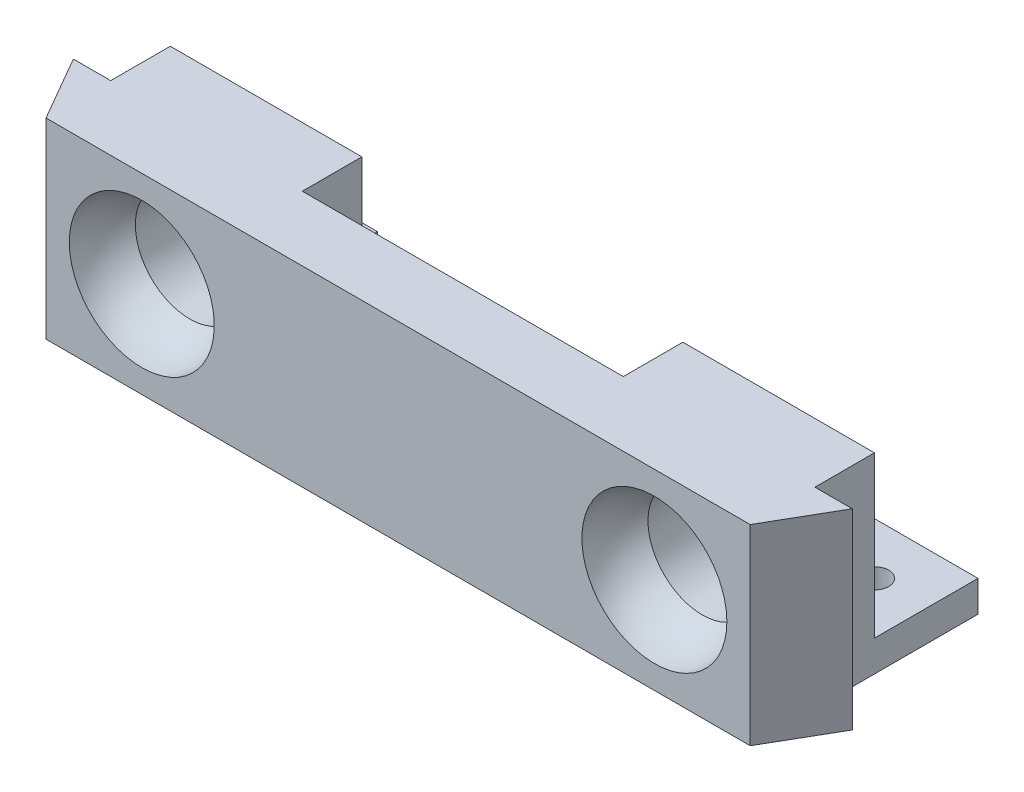
SolidWorks part; units mm, degrees
ref_plane "Front Plane" through (0, 0, 0) normal (0, 0, 1) x (1, 0, 0)
ref_plane "Top Plane" through (0, 0, 0) normal (0, 1, 0) x (1, 0, 0)
ref_plane "Right Plane" through (0, 0, 0) normal (1, 0, 0) x (0, 0, -1)
sketch "Sketch1" plane through (0, 0, 0) normal (0, 1, 0) x (1, 0, 0)
  line L0 (-34, 0) -> (-37.6084, 6.25)
  line L1 (-37.6084, 6.25) -> (-34, 6.25)
  line L2 (37.6084, 6.25) -> (34, 0)
  line L3 (34, 0) -> (-34, 0)
  line L4 (-34, 6.25) -> (-34, 12)
  line L5 (-34, 12) -> (-15.5, 12)
  line L6 (-15.5, 12) -> (-15.5, 6.25)
  line L7 (34, 6.25) -> (34, 12)
  line L8 (34, 12) -> (15.5, 12)
  line L9 (15.5, 12) -> (15.5, 6.25)
  line L11 (34, 6.25) -> (37.6084, 6.25)
  line L12 (-15.5, 6.25) -> (15.5, 6.25)
  dimension "D1" = 6.25
  dimension "D2" = 68
  dimension "D3" = 60
  dimension "D4" = 18.5
  dimension "D5" = 18.5
  dimension "D6" = 5.75
  dimension "D7" = 5.75
extrude "Boss-Extrude1" add sketch "Sketch1" along normal blind 18.5
ref_plane "Plane1" through (0, 9.25, 0) normal (0, 1, 0) x (1, 0, 0)
sketch "Sketch2" plane through (0, 9.25, 0) normal (0, 1, 0) x (1, 0, 0)
  line L0 (-24.75, 35.7158) -> (-24.75, -11.7158) construction
  line L1 (-24.75, 12) -> (-24.75, 0)
  line L2 (-15.5, 12) -> (-34, 12) construction
  line L3 (-24.75, 12) -> (-30, 12)
  line L4 (-30, 12) -> (-30, 4.6301)
  line L5 (-24.75, 0) -> (-31.75, 0)
  line L6 (-34, 0) -> (34, 0) construction
  arc A0 (-31.75, 0) -> (-30, 4.6301) centre (-24.75, 0) cw
  point P4 (-24.75, 12)
  dimension "D3" = 7
  dimension "D1" = 10.5
  dimension "D2" = 14
revolve "Cut-Revolve1" cut sketch "Sketch2" angle 360 about L0
mirror "Mirror1" about plane through (0, 0, 0) normal (1, 0, 0) of "Cut-Revolve1"
sketch "Sketch3" plane through (0, 0, 0) normal (0, 1, 0) x (1, 0, 0)
  line L0 (-34, 12) -> (-34, 22)
  line L1 (-34, 22) -> (-24, 22)
  line L2 (-24, 22) -> (-24, 12)
  line L3 (-15.5, 12) -> (-34, 12) construction
  line L4 (-24, 12) -> (-34, 12)
  line L5 (24, 12) -> (24, 22)
  line L6 (34, 12) -> (15.5, 12) construction
  line L7 (24, 22) -> (34, 22)
  line L8 (34, 22) -> (34, 12)
  line L9 (34, 12) -> (24, 12)
  dimension "D1" = 10
  dimension "D2" = 10
  dimension "D3" = 10
  dimension "D4" = 10
extrude "Boss-Extrude2" add sketch "Sketch3" along normal blind 3
sketch "Sketch5" plane through (0, 3, 0) normal (0, 1, 0) x (1, 0, 0)
  line L0 (-34, 22) -> (-34, 12) construction
  line L1 (-24, 22) -> (-34, 22) construction
  circle A0 centre (-29, 17) radius 1.375
  dimension "D3" = 2.75
  dimension "D1" = 5
  dimension "D2" = 5
extrude "Cut-Extrude1" cut sketch "Sketch5" against normal blind 3
mirror "Mirror2" about plane through (0, 0, 0) normal (1, 0, 0) of "Cut-Extrude1"
